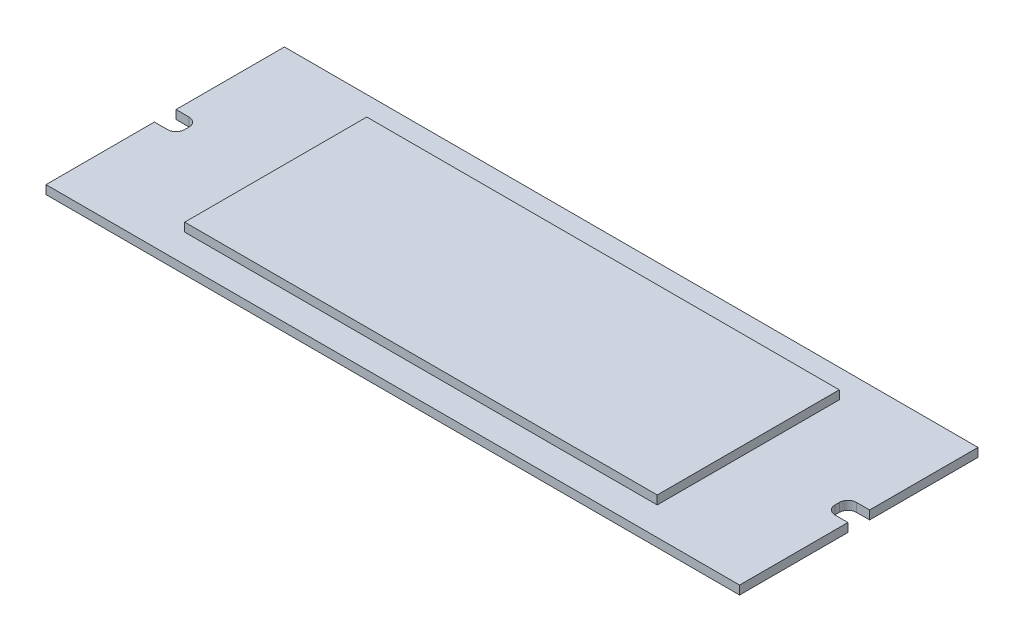
SolidWorks part; units mm, degrees
ref_plane "Front Plane" through (0, 0, 0) normal (0, 0, 1) x (1, 0, 0)
ref_plane "Top Plane" through (0, 0, 0) normal (0, 1, 0) x (1, 0, 0)
ref_plane "Right Plane" through (0, 0, 0) normal (1, 0, 0) x (0, 0, -1)
sketch "Sketch1" plane through (0, 0, 0) normal (0, 1, 0) x (1, 0, 0)
  line L1 (-58.9711, 27.1091) -> (101.0289, 27.1091)
  line L2 (-58.9711, 27.1091) -> (-58.9711, -27.8909)
  line L3 (-58.9711, -27.8909) -> (101.0289, -27.8909)
  line L4 (101.0289, 27.1091) -> (101.0289, -27.8909)
  dimension "D1" = 160
  dimension "D2" = 55
extrude "Boss-Extrude1" add sketch "Sketch1" along normal blind 2
sketch "Sketch2" plane through (0, 2, 0) normal (0, 1, 0) x (1, 0, 0)
  line L0 (-58.9711, -27.8909) -> (101.0289, -27.8909) construction
  line L1 (-33.4711, -21.3909) -> (75.5289, -21.3909)
  line L2 (-33.4711, -21.3909) -> (-33.4711, 20.6091)
  line L3 (-33.4711, 20.6091) -> (75.5289, 20.6091)
  line L4 (75.5289, -21.3909) -> (75.5289, 20.6091)
  line L5 (101.0289, -27.8909) -> (101.0289, 27.1091) construction
  point P4 (21.0289, -27.8909)
  point P5 (101.0289, -0.3909)
  point P8 (75.5289, -0.3909)
  point P11 (21.0289, -21.3909)
  dimension "D1" = 42
  dimension "D2" = 109
extrude "Boss-Extrude2" add sketch "Sketch2" along normal blind 2
sketch "Sketch3" plane through (0, 2, 0) normal (0, 1, 0) x (1, 0, 0)
  line L0 (-58.9711, 27.1091) -> (-58.9711, -27.8909) construction
  line L1 (-58.9711, 2.1091) -> (-55.9711, 2.1091)
  line L2 (-58.9711, 2.1091) -> (-58.9711, -2.8909)
  line L3 (-58.9711, -2.8909) -> (-55.9711, -2.8909)
  line L4 (-53.9711, 0.1091) -> (-53.9711, -0.8909)
  line L5 (101.0289, -27.8909) -> (101.0289, 27.1091) construction
  line L6 (101.0289, 2.1091) -> (98.0289, 2.1091)
  line L7 (101.0289, 2.1091) -> (101.0289, -2.8909)
  line L8 (101.0289, -2.8909) -> (98.0289, -2.8909)
  line L9 (96.0289, 0.1091) -> (96.0289, -0.8909)
  arc A0 (98.0289, -2.8909) -> (96.0289, -0.8909) centre (98.0289, -0.8909) cw
  arc A1 (98.0289, 2.1091) -> (96.0289, 0.1091) centre (98.0289, 0.1091) ccw
  arc A2 (-55.9711, -2.8909) -> (-53.9711, -0.8909) centre (-55.9711, -0.8909) ccw
  arc A3 (-55.9711, 2.1091) -> (-53.9711, 0.1091) centre (-55.9711, 0.1091) cw
  point P12 (-58.9711, -0.3909)
  point P13 (-58.9711, -0.3909)
  point P14 (101.0289, -0.3909)
  point P15 (101.0289, -0.3909)
  point P18 (96.0289, -2.8909)
  point P21 (96.0289, 2.1091)
  point P24 (-53.9711, -2.8909)
  point P27 (-53.9711, 2.1091)
  dimension "D5" = 2
  dimension "D1" = 150
  dimension "D2" = 5
  dimension "D3" = 5
  dimension "D4" = 5
extrude "Cut-Extrude1" cut sketch "Sketch3" against normal blind 2
